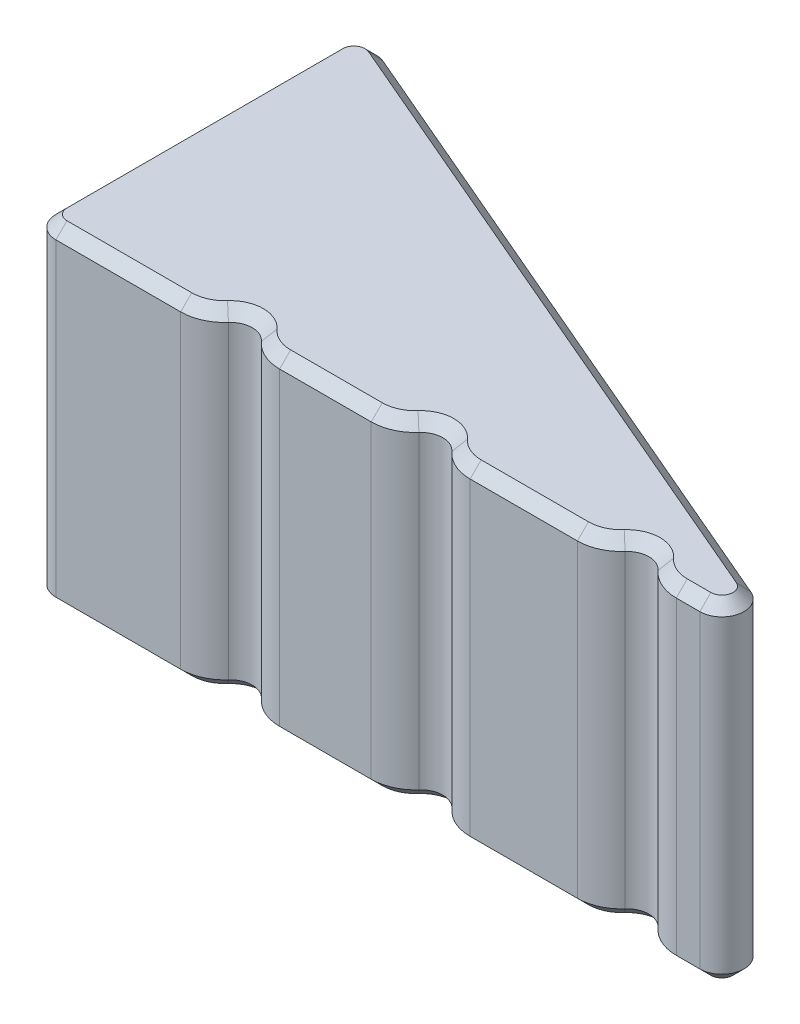
SolidWorks part; units mm, degrees
ref_plane "Front Plane" through (0, 0, 0) normal (0, 0, 1) x (1, 0, 0)
ref_plane "Top Plane" through (0, 0, 0) normal (0, 1, 0) x (1, 0, 0)
ref_plane "Right Plane" through (0, 0, 0) normal (1, 0, 0) x (0, 0, -1)
sketch "Sketch1" plane through (0, 0, 0) normal (0, 1, 0) x (1, 0, 0)
  line L0 (-97.9273, 41.9689) -> (77.0727, -33.0311)
  line L2 (-97.9273, 41.9689) -> (-97.9273, -33.0311)
  line L3 (-97.9273, -33.0311) -> (-64.6961, -33.0311)
  line L5 (-97.9273, 41.9689) -> (77.0727, -33.0311) construction
  line L6 (-97.9273, -33.0311) -> (0, 0) construction
  line L7 (-42.3355, -33.0311) -> (-21.6077, -33.0311)
  line L8 (0.753, -33.0311) -> (25.0243, -33.0311)
  line L9 (47.3849, -33.0311) -> (77.0727, -33.0311)
  arc A0 (-6.7006, -29.6978) -> (-14.1541, -29.6978) centre (-10.4273, -33.0311) ccw
  arc A1 (-49.789, -29.6978) -> (-57.2426, -29.6978) centre (-53.5158, -33.0311) ccw
  arc A2 (39.9314, -29.6978) -> (32.4778, -29.6978) centre (36.2046, -33.0311) ccw
  arc A3 (39.9314, -29.6978) -> (47.3849, -33.0311) centre (47.3849, -23.0311) ccw
  arc A4 (32.4778, -29.6978) -> (25.0243, -33.0311) centre (25.0243, -23.0311) cw
  arc A5 (-6.7006, -29.6978) -> (0.753, -33.0311) centre (0.753, -23.0311) ccw
  arc A6 (-14.1541, -29.6978) -> (-21.6077, -33.0311) centre (-21.6077, -23.0311) cw
  arc A7 (-49.789, -29.6978) -> (-42.3355, -33.0311) centre (-42.3355, -23.0311) ccw
  arc A8 (-57.2426, -29.6978) -> (-64.6961, -33.0311) centre (-64.6961, -23.0311) cw
  point P0 (0, 0)
  point P17 (41.2046, -33.0311)
  point P22 (-5.4273, -33.0311)
  point P27 (-48.5158, -33.0311)
  dimension "D3" = 10
  dimension "D1" = 75
  dimension "D2" = 175
extrude "Boss-Extrude1" add sketch "Sketch1" along normal mid plane 75
fillet "Fillet1" radius 5 3 edges at (-97.9273, 0, 33.0311) (-97.9273, 0, -41.9689) (77.0727, 0, 33.0311)
chamfer "Chamfer1" distance 2.5 angle 45 36 edges at (-97.9273, 37.5, -3.1775) (-18.1376, 37.5, -7.7732) (-78.8117, 37.5, 33.0311) (-18.1376, -37.5, -7.7732) (-97.9273, -37.5, -3.1775) (-78.8117, -37.5, 33.0311) (-96.4629, 37.5, 31.5667) (-95.6798, 37.5, -38.5604) (-95.6798, -37.5, -38.5604) (-96.4629, -37.5, 31.5667) (50.049, 37.5, 33.0311) (43.3025, 37.5, 32.1598) (36.2046, 37.5, 28.0311) (29.1067, 37.5, 32.1598) (12.8886, 37.5, 33.0311) (-3.3295, 37.5, 32.1598) (-10.4273, 37.5, 28.0311) (-17.5252, 37.5, 32.1598) (-31.9716, 37.5, 33.0311) (-46.4179, 37.5, 32.1598) (-53.5158, 37.5, 28.0311) (-60.6137, 37.5, 32.1598) (-60.6137, -37.5, 32.1598) (-53.5158, -37.5, 28.0311) (-46.4179, -37.5, 32.1598) (-31.9716, -37.5, 33.0311) (-17.5252, -37.5, 32.1598) (-10.4273, -37.5, 28.0311) (-3.3295, -37.5, 32.1598) (12.8886, -37.5, 33.0311) (29.1067, -37.5, 32.1598) (36.2046, -37.5, 28.0311) (43.3025, -37.5, 32.1598) (50.049, -37.5, 33.0311) (57.6109, 37.5, 29.0365) (57.6109, -37.5, 29.0365)
